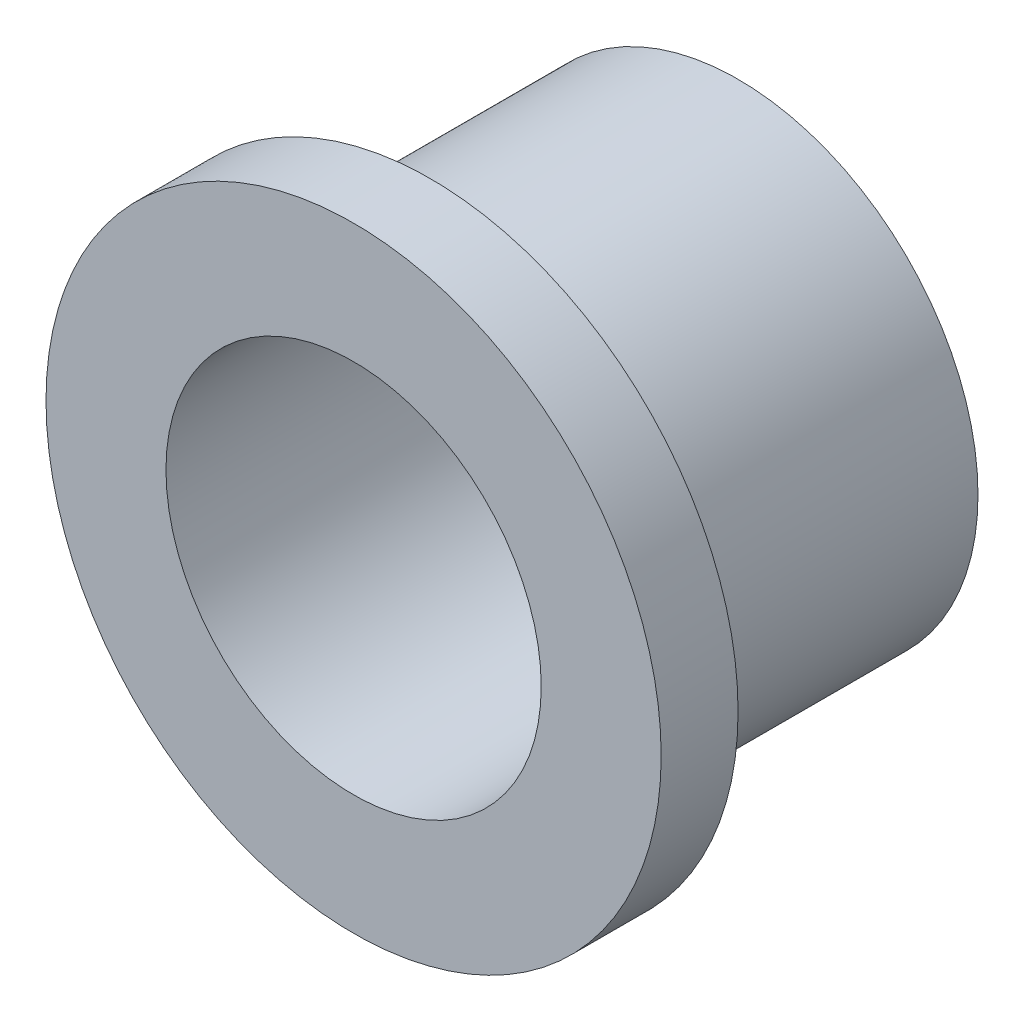
SolidWorks part; units mm, degrees
ref_plane "Front Plane" through (0, 0, 0) normal (0, 0, 1) x (1, 0, 0)
ref_plane "Top Plane" through (0, 0, 0) normal (0, 1, 0) x (1, 0, 0)
ref_plane "Right Plane" through (0, 0, 0) normal (1, 0, 0) x (0, 0, -1)
sketch "Sketch1" plane through (0, 0, 0) normal (0, 0, 1) x (1, 0, 0)
  circle A0 centre (0, 0) radius 3.9
  dimension "D1" = 7.8
extrude "Boss-Extrude1" add sketch "Sketch1" along normal blind 5
sketch "Sketch2" plane through (0, 0, 5) normal (0, 0, 1) x (1, 0, 0)
  circle A0 centre (0, 0) radius 5
  dimension "D1" = 10
extrude "Boss-Extrude2" add sketch "Sketch2" along normal blind 1.25
sketch "Sketch3" plane through (0, 0, 0) normal (0, 0, -1) x (-1, 0, 0)
  circle A0 centre (0, 0) radius 3.05
  dimension "D1" = 6.1
extrude "Cut-Extrude2" cut sketch "Sketch3" against normal through all
